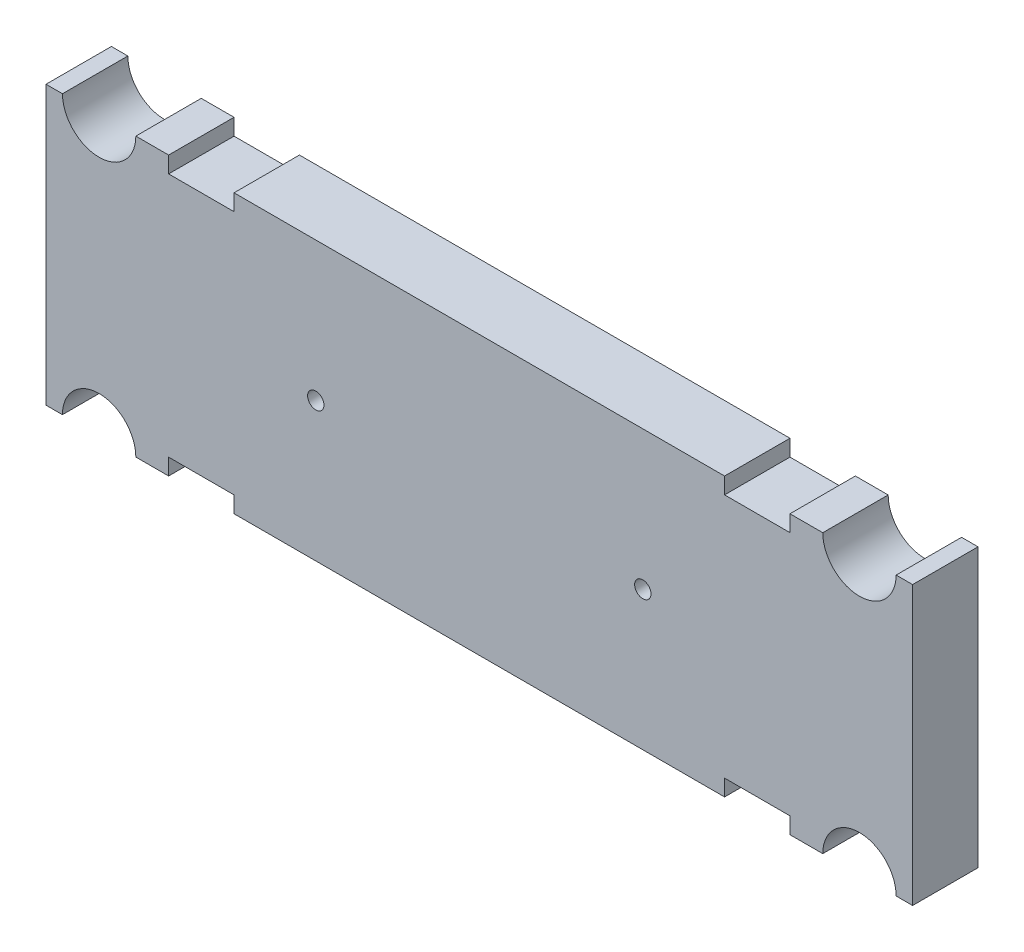
SolidWorks part; units mm, degrees
ref_plane "Ebene vorne" through (0, 0, 0) normal (0, 0, 1) x (1, 0, 0)
ref_plane "Ebene oben" through (0, 0, 0) normal (0, 1, 0) x (1, 0, 0)
ref_plane "Ebene rechts" through (0, 0, 0) normal (1, 0, 0) x (0, 0, -1)
sketch "Skizze1" plane through (0, 0, 0) normal (0, 0, 1) x (1, 0, 0)
  line L0 (0, 31.458) -> (0, -31.508) construction
  line L1 (26.5, 8.5) -> (25.4936, 8.5)
  line L2 (26.5, 8.5) -> (26.5, -8.5)
  line L3 (26.5, -8.5) -> (25.4936, -8.5)
  line L4 (-26.5, 8.5) -> (-26.5, -8.5)
  line L5 (26.5, 8.5) -> (-26.5, -8.5) construction
  line L6 (26.5, -8.5) -> (-26.5, 8.5) construction
  line L7 (-55.2644, 0) -> (51.2854, 0) construction
  line L8 (-25.4936, 8.5) -> (-26.5, 8.5)
  line L9 (-25.4936, -8.5) -> (-26.5, -8.5)
  line L10 (21.0064, -8.5) -> (19, -8.5)
  line L11 (21.0064, 8.5) -> (19, 8.5)
  line L12 (-15, -8.5) -> (-15, -7.5)
  line L14 (-19, 8.5) -> (-19, 7.5)
  line L15 (-19, 7.5) -> (-15, 7.5)
  line L16 (-15, 8.5) -> (-15, 7.5)
  line L17 (-19, -7.5) -> (-15, -7.5)
  line L18 (-19, -8.5) -> (-19, -7.5)
  line L21 (19, -8.5) -> (19, -7.5)
  line L22 (19, -7.5) -> (15, -7.5)
  line L23 (15, 8.5) -> (15, 7.5)
  line L24 (19, 7.5) -> (15, 7.5)
  line L25 (19, 8.5) -> (19, 7.5)
  line L27 (15, -8.5) -> (15, -7.5)
  line L28 (-19, 8.5) -> (-21.0064, 8.5)
  line L29 (-19, -8.5) -> (-21.0064, -8.5)
  line L30 (15, 8.5) -> (-15, 8.5)
  line L31 (15, -8.5) -> (-15, -8.5)
  arc A0 (-25.4936, 8.5) -> (-21.0064, 8.5) centre (-23.25, 8.5) ccw
  arc A1 (-25.4936, -8.5) -> (-21.0064, -8.5) centre (-23.25, -8.5) cw
  arc A2 (25.4936, -8.5) -> (21.0064, -8.5) centre (23.25, -8.5) ccw
  arc A3 (25.4936, 8.5) -> (21.0064, 8.5) centre (23.25, 8.5) cw
  point P0 (0, 0)
  dimension "D3" = 2.2436
  dimension "D1" = 17
  dimension "D2" = 53
  dimension "D4" = 3.25
  dimension "D5" = 1
  dimension "D6" = 4
  dimension "D7" = 15
extrude "Aufsatz-Linear austragen1" add sketch "Skizze1" along normal blind 4 contours L11 L25 L24 L23 L30 L16 L15 L14 L28 A0 L8 L4 L9 A1 L29 L18 L17 L12 L31 L27 L22 L21 L10 A2 L3 L2 L1 A3
sketch "Skizze2" plane through (0, 0, 4) normal (0, 0, 1) x (1, 0, 0)
  line L0 (-45.2592, 0) -> (47.4138, 0) construction
  line L1 (0, 25.4927) -> (0, -24.5875) construction
  circle A0 centre (-10, 0) radius 0.5
  circle A1 centre (10, 0) radius 0.5
  dimension "D1" = 1
  dimension "D2" = 20
extrude "Schnitt-Linear austragen1" cut sketch "Skizze2" against normal up to next
